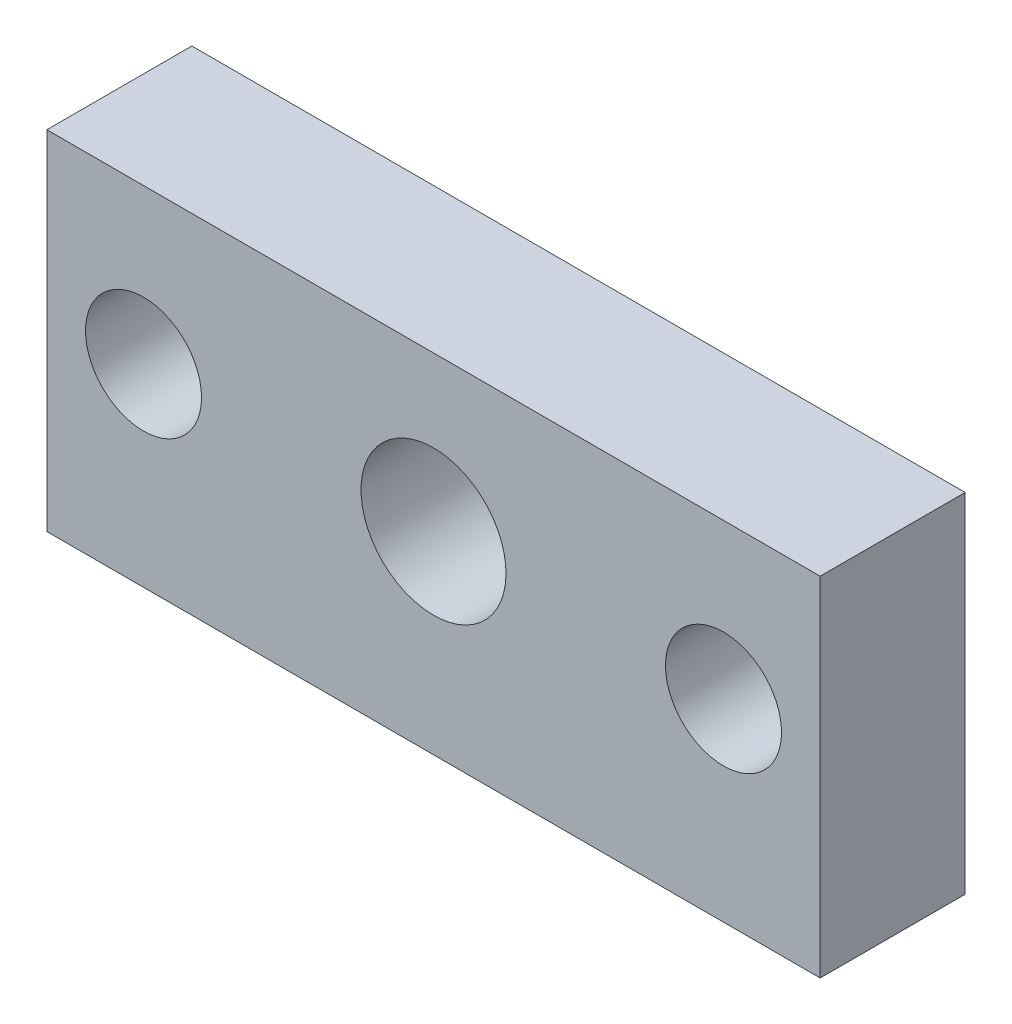
SolidWorks part; units mm, degrees
ref_plane "前视基准面" through (0, 0, 0) normal (0, 0, 1) x (1, 0, 0)
ref_plane "上视基准面" through (0, 0, 0) normal (0, 1, 0) x (1, 0, 0)
ref_plane "右视基准面" through (0, 0, 0) normal (1, 0, 0) x (0, 0, -1)
sketch "草图1" plane through (0, 0, 0) normal (0, 0, 1) x (1, 0, 0)
  line L0 (-67.5556, 4.8889) -> (121.3333, 4.8889) construction
  line L1 (-30.6667, 20.8889) -> (49.3333, 20.8889)
  line L2 (-30.6667, 20.8889) -> (-30.6667, -15.1111)
  line L3 (-30.6667, -15.1111) -> (49.3333, -15.1111)
  line L4 (49.3333, 20.8889) -> (49.3333, -15.1111)
  line L5 (9.3333, 66.6667) -> (9.3333, -67.5556) construction
  circle A0 centre (-20.6667, 4.8889) radius 6
  circle A1 centre (9.3333, 4.8889) radius 7.5
  circle A2 centre (39.3333, 4.8889) radius 6
  dimension "D4" = 12
  dimension "D5" = 15
  dimension "D6" = 60
  dimension "D1" = 80
  dimension "D2" = 36
  dimension "D3" = 20
extrude "凸台-拉伸1" add sketch "草图1" along normal blind 15
